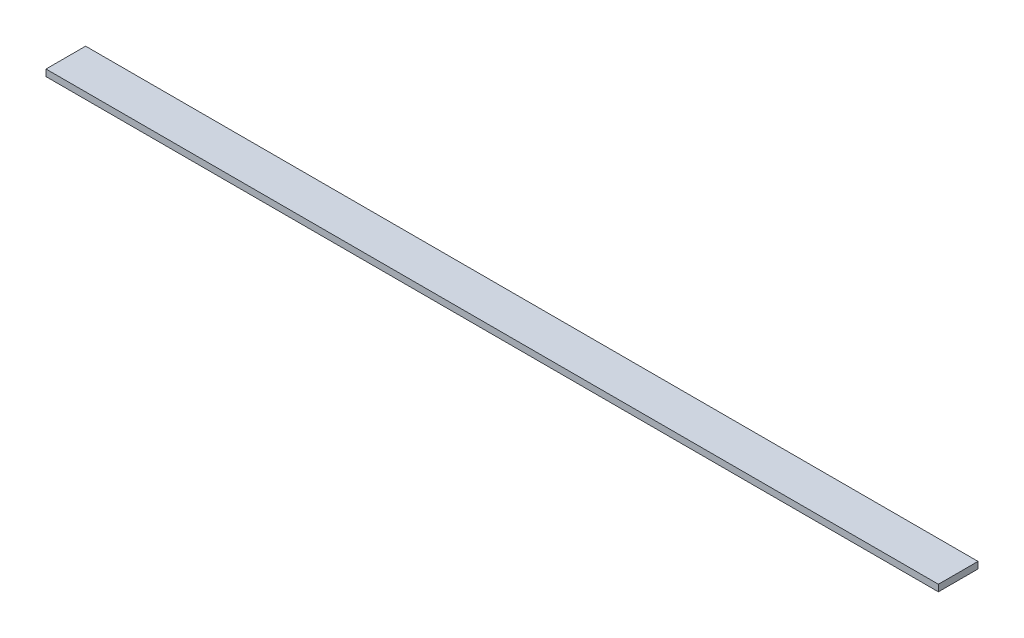
SolidWorks part; units mm, degrees
ref_plane "Front Plane" through (0, 0, 0) normal (0, 0, 1) x (1, 0, 0)
ref_plane "Top Plane" through (0, 0, 0) normal (0, 1, 0) x (1, 0, 0)
ref_plane "Right Plane" through (0, 0, 0) normal (1, 0, 0) x (0, 0, -1)
sketch "Sketch7" plane through (0, 0, 0) normal (0, 1, 0) x (1, 0, 0)
  line L1 (0, 0) -> (-429.26, 0)
  line L2 (0, 0) -> (0, -19.05)
  line L3 (0, -19.05) -> (-429.26, -19.05)
  line L4 (-429.26, 0) -> (-429.26, -19.05)
  dimension "D1" = 429.26
  dimension "3/4" = 19.05
extrude "Boss-Extrude5" add sketch "Sketch7" along normal blind 3.175
